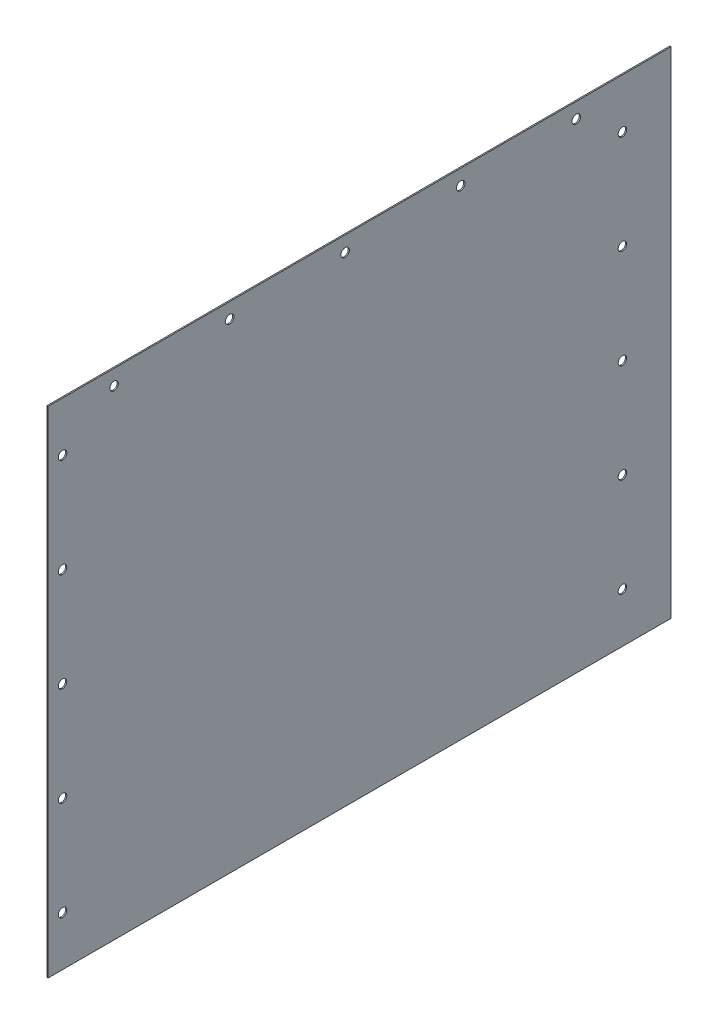
SolidWorks part; units mm, degrees
material "AISI 316 Stainless Steel Sheet (SS)"
ref_plane "Front Plane" through (0, 0, 0) normal (0, 0, 1) x (1, 0, 0)
ref_plane "Top Plane" through (0, 0, 0) normal (0, 1, 0) x (1, 0, 0)
ref_plane "Right Plane" through (0, 0, 0) normal (1, 0, 0) x (0, 0, -1)
sketch "Sketch1" plane through (0, 0, 0) normal (1, 0, 0) x (0, 0, -1)
  line L1 (-239.6998, -190.5) -> (239.6998, -190.5)
  line L2 (-239.6998, -190.5) -> (-239.6998, 190.5)
  line L3 (-239.6998, 190.5) -> (239.6998, 190.5)
  line L4 (239.6998, -190.5) -> (239.6998, 190.5)
  line L5 (-239.6998, -190.5) -> (239.6998, 190.5) construction
  line L6 (-239.6998, 190.5) -> (239.6998, -190.5) construction
  point P0 (0, 0)
  dimension "D1" = 479.3996
  dimension "D2" = 381
extrude "Boss-Extrude1" add sketch "Sketch1" along normal blind 0.9144
hole_wizard "F (0.257) Diameter Hole1" positions "Sketch2" profile "Sketch3" hole size "F" standard "ANSI Inch" end condition through all
sketch "Sketch2" plane through (0, 0, 0) normal (-1, 0, 0) x (0, 0, 1)
  point P0 (188.8998, 178.7144)
  point P2 (99.9998, 178.7144)
  point P5 (11.0998, 178.7144)
  point P8 (-77.8002, 178.7144)
  point P11 (-166.7002, 178.7144)
sketch "Sketch3" plane through (0, 178.7144, 188.8998) normal (0, 1, 0) x (0, 0, 1)
  line L0 (0, 0) -> (0, 0.9144)
  line L1 (0, 0.9144) -> (3.2639, 0.9144)
  line L2 (3.2639, 0.9144) -> (3.2639, 0)
  line L5 (3.2639, 0) -> (0, 0)
  line L11 (0, -6.35) -> (0, 107.95) construction
  dimension "Thru Hole Dia." = 6.5278
  dimension "Thru Hole Depth" = 0.9144
sketch "Sketch4" plane through (0.9144, 0, 0) normal (1, 0, 0) x (0, 0, -1)
  line L0 (-239.6998, 190.5) -> (-239.6998, -190.5) construction
  line L1 (239.6998, 190.5) -> (-239.6998, 190.5) construction
  circle A0 centre (-228.6, 152.4) radius 3.2639
  circle A1 centre (-228.6, 76.2) radius 3.2639
  circle A2 centre (-228.6, 0) radius 3.2639
  circle A3 centre (-228.6, -76.2) radius 3.2639
  circle A4 centre (-228.6, -152.4) radius 3.2639
  dimension "D1" = 11.0998
  dimension "D2" = 6.5278
  dimension "D3" = 38.1
  dimension "D4" = 6.5278
  dimension "D5" = 6.5278
  dimension "D6" = 6.5278
  dimension "D7" = 6.5278
  dimension "D8" = 76.2
  dimension "D10" = 76.2
  dimension "D11" = 76.2
  dimension "D9" = 76.2
extrude "Cut-Extrude1" cut sketch "Sketch4" against normal blind 2.54
sketch "Sketch5" plane through (0, 0, 0) normal (-1, 0, 0) x (0, 0, 1)
  line L0 (-239.6998, -190.5) -> (-239.6998, 190.5) construction
  line L1 (-239.6998, 190.5) -> (239.6998, 190.5) construction
  circle A0 centre (-202.2856, 152.4) radius 3.2639
  circle A1 centre (-202.2856, 76.2) radius 3.2639
  circle A2 centre (-202.2856, 0) radius 3.2639
  circle A3 centre (-202.2856, -76.2) radius 3.2639
  circle A4 centre (-202.2856, -152.4) radius 3.2639
  dimension "D1" = 37.4142
  dimension "D2" = 38.1
  dimension "D3" = 6.5278
  dimension "D4" = 6.5278
  dimension "D5" = 6.5278
  dimension "D6" = 6.5278
  dimension "D7" = 6.5278
  dimension "D9" = 76.2
  dimension "D10" = 76.2
  dimension "D11" = 76.2
  dimension "D8" = 76.2
extrude "Cut-Extrude2" cut sketch "Sketch5" against normal blind 2.54
